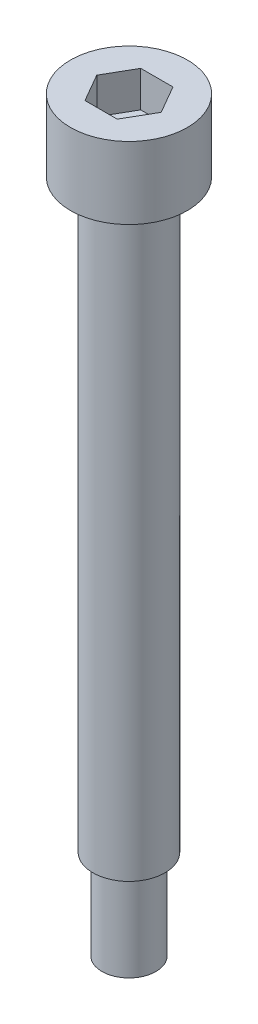
SolidWorks part; units mm, degrees
material "AISI 304"
ref_plane "前视基准面" through (0, 0, 0) normal (0, 0, 1) x (1, 0, 0)
ref_plane "上视基准面" through (0, 0, 0) normal (0, 1, 0) x (1, 0, 0)
ref_plane "右视基准面" through (0, 0, 0) normal (1, 0, 0) x (0, 0, -1)
sketch "草图1" plane through (0, 0, 0) normal (0, 1, 0) x (1, 0, 0)
  circle A0 centre (0, 0) radius 6.5
  dimension "D1" = 13
extrude "杯头" add sketch "草图1" along normal blind 8
sketch "草图2" plane through (0, 8, 0) normal (0, 1, 0) x (1, 0, 0)
  line L1 (3.5796, 0) -> (1.7898, 3.1)
  line L2 (1.7898, 3.1) -> (-1.7898, 3.1)
  line L3 (-1.7898, 3.1) -> (-3.5796, 0)
  line L4 (-3.5796, 0) -> (-1.7898, -3.1)
  line L5 (-1.7898, -3.1) -> (1.7898, -3.1)
  line L6 (1.7898, -3.1) -> (3.5796, 0)
  circle A0 centre (0, 0) radius 3.1 construction
  dimension "D1" = 6.2
extrude "内六角口" cut sketch "草图2" against normal blind 4
sketch "草图3" plane through (0, 0, 0) normal (0, -1, 0) x (1, 0, 0)
  circle A0 centre (0, 0) radius 4
  dimension "D1" = 8
extrude "光轴" add sketch "草图3" along normal blind 65
sketch "草图4" plane through (0, -65, 0) normal (0, -1, 0) x (1, 0, 0)
  circle A0 centre (0, 0) radius 3
  dimension "D1" = 6
extrude "M6螺纹" add sketch "草图4" along normal blind 10
